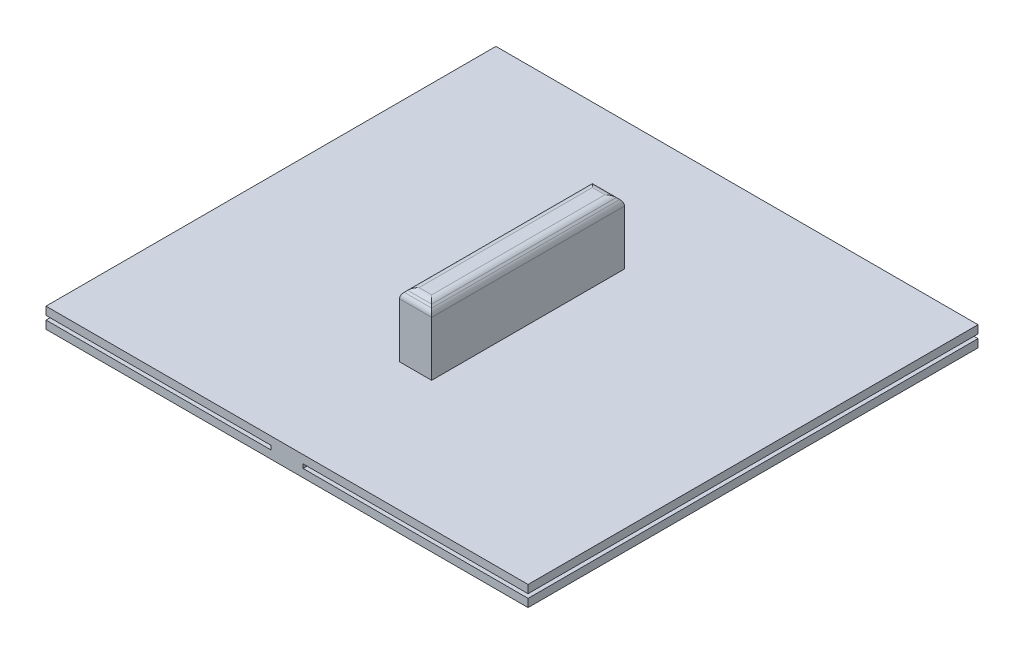
SolidWorks part; units mm, degrees
ref_plane "Front Plane" through (0, 0, 0) normal (0, 0, 1) x (1, 0, 0)
ref_plane "Top Plane" through (0, 0, 0) normal (0, 1, 0) x (1, 0, 0)
ref_plane "Right Plane" through (0, 0, 0) normal (1, 0, 0) x (0, 0, -1)
sketch "Sketch1" plane through (0, 0, 0) normal (0, 0, 1) x (1, 0, 0)
  line L0 (-1.27, -0.635) -> (-1.27, 5.3975) construction
  line L1 (-19.05, -0.3175) -> (19.05, -0.3175) construction
  line L2 (-19.05, -0.3175) -> (-19.05, 0.3175)
  line L3 (-19.05, 0.3175) -> (19.05, 0.3175) construction
  line L4 (19.05, -0.3175) -> (19.05, 0.3175)
  line L5 (-19.05, -0.3175) -> (19.05, 0.3175) construction
  line L6 (-19.05, 0.3175) -> (19.05, -0.3175) construction
  line L7 (-19.05, -1.27) -> (19.05, -1.27)
  line L8 (-19.05, -1.27) -> (-19.05, -0.635)
  line L9 (-19.05, -0.635) -> (19.05, -0.635) construction
  line L10 (19.05, -1.27) -> (19.05, -0.635)
  line L11 (-19.05, -1.27) -> (19.05, -0.635) construction
  line L12 (-19.05, -0.635) -> (19.05, -1.27) construction
  line L13 (-1.27, 5.3975) -> (1.27, 5.3975)
  line L14 (1.27, 5.3975) -> (1.27, -0.635) construction
  line L15 (1.27, -0.635) -> (19.05, -0.635)
  line L16 (-19.05, -0.635) -> (-1.27, -0.635)
  line L17 (-1.27, -0.635) -> (-1.27, -0.3175)
  line L18 (-1.27, -0.3175) -> (-19.05, -0.3175)
  line L19 (1.27, -0.635) -> (1.27, -0.3175)
  line L20 (1.27, -0.3175) -> (19.05, -0.3175)
  line L21 (19.05, 0.3175) -> (1.27, 0.3175)
  line L22 (1.27, 0.3175) -> (1.27, 5.3975)
  line L23 (-1.27, 5.3975) -> (-1.27, 0.3175)
  line L24 (-1.27, 0.3175) -> (-19.05, 0.3175)
  point P0 (0, 0)
  point P6 (0, -0.9525)
  point P14 (0, 5.3975)
  dimension "D1" = 38.1
  dimension "D2" = 0.635
  dimension "D3" = 0.3175
  dimension "D4" = 2.54
  dimension "D5" = 5.08
extrude "Boss-Extrude1" add sketch "Sketch1" against normal blind 35.56
sketch "Sketch2" plane through (0, 0, 0) normal (0, 0, 1) x (1, 0, 0)
  line L1 (-1.27, 5.3975) -> (1.27, 5.3975)
  line L2 (-1.27, 5.3975) -> (-1.27, 0.3175)
  line L3 (-1.27, 0.3175) -> (1.27, 0.3175)
  line L4 (1.27, 5.3975) -> (1.27, 0.3175)
extrude "Cut-Extrude1" cut sketch "Sketch2" against normal blind 10.16
sketch "Sketch3" plane through (0, 0, -35.56) normal (0, 0, -1) x (-1, 0, 0)
  line L1 (-1.27, 0.3175) -> (1.27, 0.3175)
  line L2 (-1.27, 0.3175) -> (-1.27, 5.3975)
  line L3 (-1.27, 5.3975) -> (1.27, 5.3975)
  line L4 (1.27, 0.3175) -> (1.27, 5.3975)
extrude "Cut-Extrude2" cut sketch "Sketch3" against normal blind 10.16
chamfer "Chamfer1" distance 0.508 angle 45 4 edges at (1.27, 5.3975, -17.78) (0, 5.3975, -10.16) (-1.27, 5.3975, -17.78) (0, 5.3975, -25.4)
fillet "Fillet1" radius 0.635 8 edges at (-0.762, 5.3975, -17.78) (0, 5.3975, -24.892) (0.762, 5.3975, -17.78) (0, 5.3975, -10.668) (0, 4.8895, -25.4) (0, 4.8895, -10.16) (-1.27, 4.8895, -17.78) (1.27, 4.8895, -17.78)
